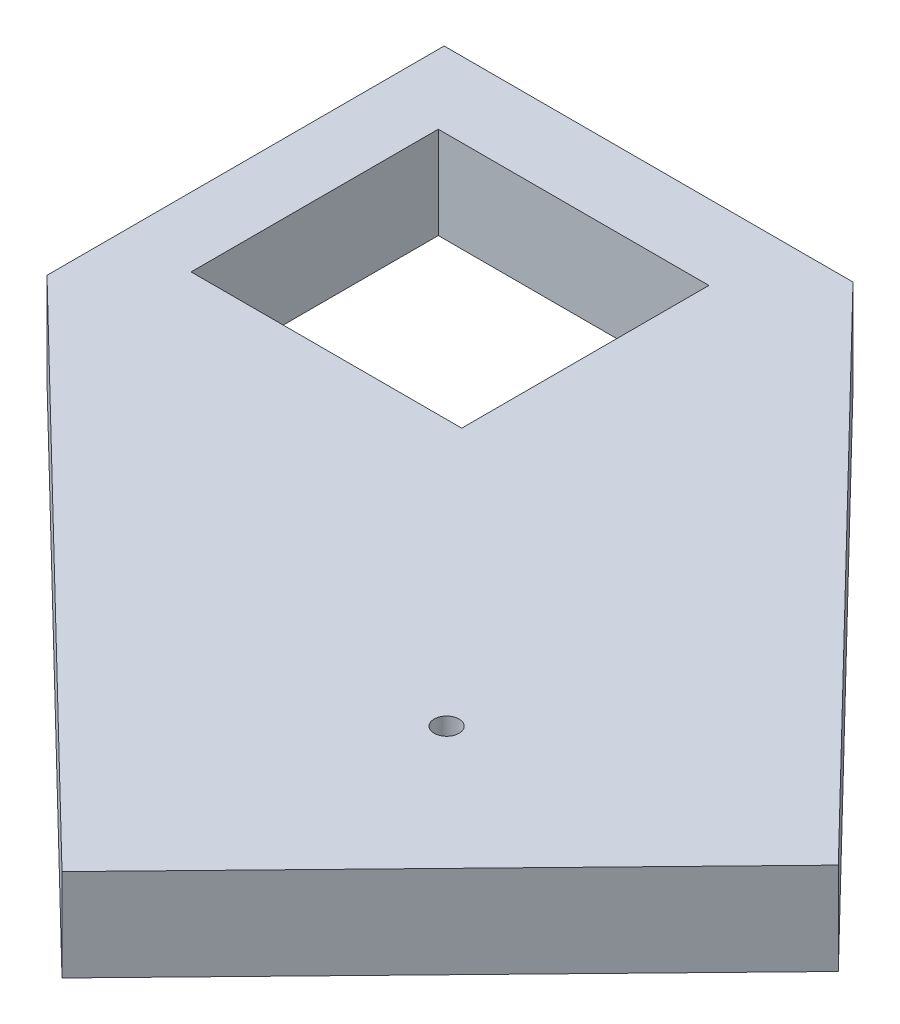
SolidWorks part; units mm, degrees
ref_plane "Front Plane" through (0, 0, 0) normal (0, 0, 1) x (1, 0, 0)
ref_plane "Top Plane" through (0, 0, 0) normal (0, 1, 0) x (1, 0, 0)
ref_plane "Right Plane" through (0, 0, 0) normal (1, 0, 0) x (0, 0, -1)
sketch "Sketch1" plane through (0, 0, 0) normal (0, 1, 0) x (1, 0, 0)
  line L0 (-44.38, -43.1084) -> (69.3631, -153.5923)
  line L1 (-29.3747, 26.8315) -> (29.3747, 26.8315)
  line L2 (-29.3747, 26.8315) -> (-29.3747, -26.8315)
  line L3 (-29.3747, -26.8315) -> (29.3747, -26.8315)
  line L4 (29.3747, 26.8315) -> (29.3747, -26.8315)
  line L5 (-29.3747, 26.8315) -> (29.3747, -26.8315) construction
  line L6 (-29.3747, -26.8315) -> (29.3747, 26.8315) construction
  line L7 (-44.38, 43.1084) -> (44.38, 43.1084)
  line L8 (-44.38, 43.1084) -> (-44.38, -43.1084)
  line L9 (-44.38, -43.1084) -> (44.38, -43.1084) construction
  line L10 (44.38, 43.1084) -> (44.38, -43.1084) construction
  line L11 (-44.38, 43.1084) -> (44.38, -43.1084) construction
  line L12 (-44.38, -43.1084) -> (44.38, 43.1084) construction
  line L13 (69.3631, -153.5923) -> (152.4038, -68.102)
  line L14 (152.4038, -68.102) -> (44.38, 43.1084)
  point P0 (0, 0)
  point P6 (0, 0)
extrude "Boss-Extrude1" add sketch "Sketch1" along normal blind 20 contours L13 L14 L7 L8 L0 L1 L4 L3 L2
sketch "Sketch2" plane through (0, 20, 0) normal (0, 1, 0) x (1, 0, 0)
  line L0 (152.4038, -68.102) -> (69.3631, -153.5923) construction
  line L1 (152.4038, -68.102) -> (44.38, 43.1084) construction
  line L2 (69.3631, -153.5923) -> (152.4038, -68.102) construction
  line L3 (110.8834, -110.8472) -> (83.759, -84.5) construction
  circle A0 centre (83.759, -84.5) radius 2.7
  point P10 (83.759, -84.5)
  dimension "D1" = 5.4
extrude "Cut-Extrude1" cut sketch "Sketch2" against normal blind 20
sketch "Sketch3" plane through (0, 0, 0) normal (0, -1, 0) x (1, 0, 0)
  line L0 (0, 0) -> (83.759, 84.5) construction
  circle A0 centre (83.759, 84.5) radius 15
  dimension "D1" = 30
sketch3d "3DSketch1"
  line L0 (0, 0, 0) -> (0, -79.2396, 0) construction
  line L1 (0, 0, 0) -> (83.759, 0, 84.5) construction
  line L2 (0, 0, 0) -> (83.759, 0, 84.5) construction
ref_plane "Plane1" through (0, 0, 0) normal (-0.7102, 0, 0.704) x (0.704, 0, 0.7102)
sketch "Sketch4" plane through (0, 0, 0) normal (-0.7102, 0, 0.704) x (0.704, 0, 0.7102)
  line L0 (0, 0) -> (118.9782, 0) construction
  line L2 (103.9782, 0) -> (133.9782, 0) construction
  circle A0 centre (103.9782, 0) radius 3
  point P6 (0, 0)
  dimension "D1" = 6
sweep "Cut-Sweep1" cut profiles "Sketch4" path "Sketch3"
